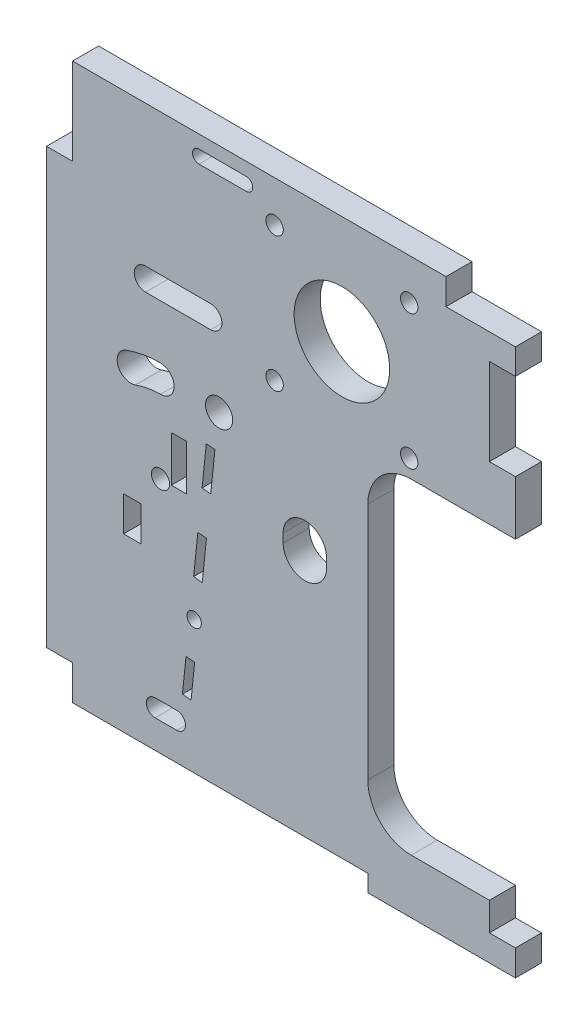
SolidWorks part; units mm, degrees
ref_plane "Face" through (0, 0, 0) normal (0, 0, 1) x (1, 0, 0)
ref_plane "Dessus" through (0, 0, 0) normal (0, 1, 0) x (1, 0, 0)
ref_plane "Droite" through (0, 0, 0) normal (1, 0, 0) x (0, 0, -1)
sketch "Esquisse1" plane through (0, 0, 0) normal (0, 0, 1) x (1, 0, 0)
  line L2 (2401.4759, -52.1041) -> (2401.4759, -46.1041)
  line L3 (2401.4759, 73.7928) -> (2395.4759, 73.7928)
  line L4 (2293.4759, -40.2072) -> (2293.4759, 59.7928)
  line L5 (2293.4759, -32.1041) -> (2293.4759, 67.8959) construction
  line L6 (2331.2759, 44.7009) -> (2331.2759, 75.2928) construction
  line L7 (2401.4759, -111.1029) -> (2401.4759, -71.1041) construction
  line L9 (2385.4759, 73.7928) -> (2395.4759, 73.7928) construction
  line L17 (2401.4759, 35.3959) -> (2401.4759, 47.8959)
  line L18 (2401.4759, 47.8959) -> (2395.4759, 47.8959)
  line L19 (2395.4759, 47.8959) -> (2395.4759, 67.8959)
  line L20 (2395.4759, 67.8959) -> (2401.4759, 67.8959)
  line L22 (2401.4759, 67.8959) -> (2401.4759, 73.7928)
  line L23 (2331.2759, 42.1009) -> (2316.2759, 42.1009) construction
  line L24 (2316.2759, 47.3009) -> (2331.2759, 47.3009) construction
  line L25 (2347.9759, 7.8959) -> (2347.9759, 9.8959) construction
  line L26 (2357.9759, 9.8959) -> (2357.9759, 7.8959) construction
  line L29 (2331.2759, 42.1009) -> (2316.2759, 42.1009)
  line L30 (2316.2759, 47.3009) -> (2331.2759, 47.3009)
  line L31 (2347.9759, 7.8959) -> (2347.9759, 9.8959)
  line L32 (2357.9759, 9.8959) -> (2357.9759, 7.8959)
  line L66 (2395.4759, -79.2072) -> (2395.4759, -39.2054) construction
  line L69 (2401.4759, -46.1041) -> (2395.4759, -46.1041)
  line L82 (2397.4759, 35.3959) -> (2377.4759, 35.3959) construction
  line L83 (2367.4759, 25.3959) -> (2367.4759, -29.6041) construction
  line L84 (2377.4759, -39.6041) -> (2397.4759, -39.6041) construction
  line L85 (2397.4759, 35.3959) -> (2377.4759, 35.3959)
  line L86 (2367.4759, 25.3959) -> (2367.4759, -29.6041)
  line L87 (2377.4759, -39.6041) -> (2395.4759, -39.6041)
  line L88 (2397.4759, 35.3959) -> (2401.4759, 35.3959)
  line L90 (2385.4759, 73.7928) -> (2385.4759, 79.7928) construction
  line L91 (2401.4759, -34.8058) -> (2407.3044, -34.8058) [skipped]
  line L92 (2395.4759, -34.8058) -> (2395.4759, -88.5967) [skipped]
  line L93 (2395.4759, -14.8058) -> (2401.4759, -14.8058) [skipped]
  line L94 (2401.4759, 6.5451) -> (2407.3044, 6.5451) [skipped]
  line L95 (2395.4759, 6.5451) -> (2395.4759, -47.2459) [skipped]
  line L96 (2395.4759, 26.5451) -> (2401.4759, 26.5451) [skipped]
  line L97 (2395.4759, -111.1029) -> (2395.4759, -151.1041) construction
  line L98 (2385.4759, 79.7928) -> (2299.4759, 79.7928)
  line L99 (2385.4759, 79.7928) -> (2395.4759, 79.7928) construction
  line L100 (2395.4759, 51.6021) -> (2395.4759, 47.8959) construction
  line L101 (2401.4759, 67.8959) -> (2395.4759, 67.8959) construction
  line L102 (2339.473, 75.2928) -> (2328.5995, 75.2928) construction
  line L103 (2339.473, 73.7928) -> (2328.5995, 73.7928)
  line L104 (2339.473, 76.7928) -> (2328.5995, 76.7928)
  line L105 (2328.5995, 75.2928) -> (2331.2759, 44.7009) construction
  line L107 (2385.4759, 79.7928) -> (2385.4759, 73.7928)
  line L108 (2385.4759, 73.7928) -> (2395.4759, 73.7928)
  line L110 (2339.473, 75.2928) -> (2331.2759, 44.7009) construction
  line L111 (2315.2259, -0.6415) -> (2315.2259, -8.6415) construction
  line L112 (2315.2259, -0.6415) -> (2315.2259, -8.6415)
  line L113 (2315.2259, -8.6415) -> (2311.2259, -8.6415)
  line L114 (2311.2259, -8.6415) -> (2311.2259, -0.6415)
  line L115 (2311.2259, -0.6415) -> (2315.2259, -0.6415)
  line L116 (2395.4759, -39.6041) -> (2395.4759, -46.1041)
  line L117 (2299.4759, -48.2072) -> (2299.4759, -40.2072)
  line L118 (2329.3029, 9.5528) -> (2330.2759, 18.8794) construction
  line L119 (2330.2759, 18.8794) -> (2332.2651, 18.6718) construction
  line L120 (2332.2651, 18.6718) -> (2331.2921, 9.3453) construction
  line L121 (2331.2921, 9.3453) -> (2329.3029, 9.5528) construction
  line L122 (2327.3569, -9.1002) -> (2328.3299, 0.2263) construction
  line L123 (2328.3299, 0.2263) -> (2330.3191, 0.0188) construction
  line L124 (2330.3191, 0.0188) -> (2329.3461, -9.3077) construction
  line L125 (2329.3461, -9.3077) -> (2327.3569, -9.1002) construction
  line L126 (2324.7759, -33.8389) -> (2325.6061, -25.8821) construction
  line L127 (2325.6061, -25.8821) -> (2327.5953, -26.0896) construction
  line L128 (2327.5953, -26.0896) -> (2326.7651, -34.0464) construction
  line L129 (2326.7651, -34.0464) -> (2324.7759, -33.8389) construction
  line L130 (2329.3029, 9.5528) -> (2330.2759, 18.8794)
  line L131 (2330.2759, 18.8794) -> (2332.2651, 18.6718)
  line L132 (2332.2651, 18.6718) -> (2331.2921, 9.3453)
  line L133 (2331.2921, 9.3453) -> (2329.3029, 9.5528)
  line L134 (2327.3569, -9.1002) -> (2328.3299, 0.2263)
  line L135 (2328.3299, 0.2263) -> (2330.3191, 0.0188)
  line L136 (2330.3191, 0.0188) -> (2329.3461, -9.3077)
  line L137 (2329.3461, -9.3077) -> (2327.3569, -9.1002)
  line L138 (2324.7759, -33.8389) -> (2325.6061, -25.8821)
  line L139 (2325.6061, -25.8821) -> (2327.5953, -26.0896)
  line L140 (2327.5953, -26.0896) -> (2326.7651, -34.0464)
  line L141 (2326.7651, -34.0464) -> (2324.7759, -33.8389)
  line L142 (2325.6061, -25.8821) -> (2329.3461, -9.3077) construction
  line L143 (2327.5953, -26.0896) -> (2327.3569, -9.1002) construction
  line L146 (2293.4759, 59.7928) -> (2299.4759, 59.7928)
  line L147 (2299.4759, 79.7928) -> (2299.4759, 59.7928)
  line L148 (2299.4759, -40.2072) -> (2293.4759, -40.2072)
  line L153 (2322.2259, 6.5647) -> (2325.7259, 6.5647)
  line L154 (2322.2259, 6.5647) -> (2322.2259, 17.0647)
  line L155 (2322.2259, 17.0647) -> (2325.7259, 17.0647)
  line L156 (2325.7259, 6.5647) -> (2325.7259, 17.0647)
  line L161 (2299.4759, -48.2072) -> (2367.4759, -48.2072)
  line L162 (2401.4759, -52.1041) -> (2367.4759, -52.1041)
  line L163 (2367.4759, -52.1041) -> (2367.4759, -48.2072)
  line L164 (2318.4759, -39.7072) -> (2323.4759, -39.7072) construction
  line L165 (2318.4759, -37.7072) -> (2323.4759, -37.7072)
  line L166 (2318.4759, -41.7072) -> (2323.4759, -41.7072)
  arc A0 (2316.2759, 47.3009) -> (2316.2759, 42.1009) centre (2316.2759, 44.7009) ccw construction
  arc A1 (2331.2759, 42.1009) -> (2331.2759, 47.3009) centre (2331.2759, 44.7009) ccw construction
  circle A2 centre (2346.0102, 70.349) radius 2 construction
  circle A3 centre (2377.0102, 70.349) radius 2 construction
  circle A4 centre (2377.0102, 39.349) radius 2 construction
  circle A5 centre (2361.5102, 54.849) radius 11 construction
  circle A6 centre (2346.0102, 39.349) radius 2 construction
  arc A7 (2357.9759, 9.8959) -> (2347.9759, 9.8959) centre (2352.9759, 9.8959) ccw construction
  arc A8 (2347.9759, 7.8959) -> (2357.9759, 7.8959) centre (2352.9759, 7.8959) ccw construction
  circle A9 centre (2333.2259, 26.5647) radius 3.125 construction
  arc A10 (2319.7259, 29.6947) -> (2311.815, 28.2998) centre (2319.7259, 6.5647) ccw construction
  arc A11 (2311.815, 28.2998) -> (2313.9561, 22.4174) centre (2312.8855, 25.3586) ccw construction
  arc A12 (2319.7259, 23.4347) -> (2319.7259, 29.6947) centre (2319.7259, 26.5647) ccw construction
  arc A13 (2319.7259, 23.4347) -> (2313.9561, 22.4174) centre (2319.7259, 6.5647) ccw construction
  arc A17 (2316.2759, 47.3009) -> (2316.2759, 42.1009) centre (2316.2759, 44.7009) ccw
  arc A18 (2331.2759, 42.1009) -> (2331.2759, 47.3009) centre (2331.2759, 44.7009) ccw
  circle A19 centre (2346.0102, 70.349) radius 2
  circle A20 centre (2377.0102, 70.349) radius 2
  circle A21 centre (2377.0102, 39.349) radius 2
  circle A22 centre (2361.5102, 54.849) radius 11
  circle A23 centre (2346.0102, 39.349) radius 2
  arc A24 (2357.9759, 9.8959) -> (2347.9759, 9.8959) centre (2352.9759, 9.8959) ccw
  arc A25 (2347.9759, 7.8959) -> (2357.9759, 7.8959) centre (2352.9759, 7.8959) ccw
  circle A26 centre (2333.2259, 26.5647) radius 3.125
  arc A27 (2319.7259, 29.6947) -> (2311.815, 28.2998) centre (2319.7259, 6.5647) ccw
  arc A28 (2311.815, 28.2998) -> (2313.9561, 22.4174) centre (2312.8855, 25.3586) ccw
  arc A29 (2319.7259, 23.4347) -> (2319.7259, 29.6947) centre (2319.7259, 26.5647) ccw
  arc A30 (2319.7259, 23.4347) -> (2313.9561, 22.4174) centre (2319.7259, 6.5647) ccw
  arc A34 (2377.4759, 35.3959) -> (2367.4759, 25.3959) centre (2377.4759, 25.3959) ccw construction
  arc A35 (2367.4759, -29.6041) -> (2377.4759, -39.6041) centre (2377.4759, -29.6041) ccw construction
  arc A36 (2377.4759, 35.3959) -> (2367.4759, 25.3959) centre (2377.4759, 25.3959) ccw
  arc A37 (2367.4759, -29.6041) -> (2377.4759, -39.6041) centre (2377.4759, -29.6041) ccw
  arc A38 (2339.473, 73.7928) -> (2339.473, 76.7928) centre (2339.473, 75.2928) ccw
  arc A39 (2328.5995, 76.7928) -> (2328.5995, 73.7928) centre (2328.5995, 75.2928) ccw
  circle A40 centre (2319.7259, 6.5647) radius 2.1
  circle A41 centre (2319.7259, -9.6415) radius 2.1 construction
  circle A42 centre (2327.4761, -17.5949) radius 1.65
  arc A44 (2318.4759, -37.7072) -> (2318.4759, -41.7072) centre (2318.4759, -39.7072) ccw
  arc A45 (2323.4759, -41.7072) -> (2323.4759, -37.7072) centre (2323.4759, -39.7072) ccw
  point P3 (0, 0)
  point P8 (2334.0363, 75.2928)
  point P73 (2401.6004, -52.1041)
  point P74 (2401.4759, -52.1041)
  point P143 (2320.9759, -39.7072)
  dimension "D8" = 3.3
  dimension "D1" = 20
  dimension "D2" = 3
  dimension "D3" = 3
  dimension "D4" = 3
  dimension "D5" = 15
  dimension "D6" = 20
  dimension "D7" = 4
  dimension "D9" = 6
  dimension "D10" = 6.5
  dimension "D13" = 3.5
  dimension "D14" = 10.5
  dimension "D15" = 6
  dimension "D16" = 8.5
  dimension "D17" = 8
  dimension "D18" = 3.8969
  dimension "D19" = 4
  dimension "D20" = 5
  dimension "D21" = 24
extrude "Boss.-Extru.1" add sketch "Esquisse1" against normal blind 6
